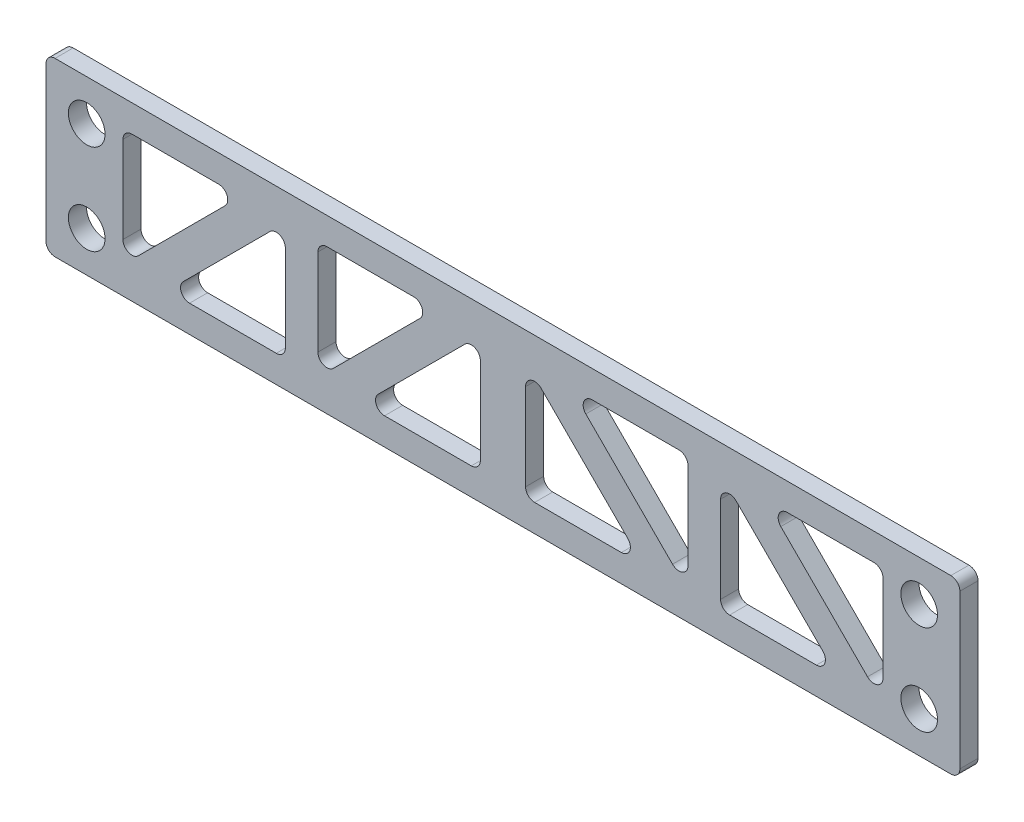
SolidWorks part; units mm, degrees
material "Thornel Mat VMA"
ref_plane "前视基准面" through (0, 0, 0) normal (0, 0, 1) x (1, 0, 0)
ref_plane "上视基准面" through (0, 0, 0) normal (0, 1, 0) x (1, 0, 0)
ref_plane "右视基准面" through (0, 0, 0) normal (1, 0, 0) x (0, 0, -1)
other "Configuration Table"
sketch "草图1" plane through (0, 0, 0) normal (0, 0, 1) x (1, 0, 0)
  line L1 (-46, -5) -> (46, -5) construction
  line L2 (-46, -5) -> (-46, 5) construction
  line L3 (-46, 5) -> (46, 5) construction
  line L4 (46, -5) -> (46, 5) construction
  line L5 (-46, -5) -> (46, 5) construction
  line L6 (-46, 5) -> (46, -5) construction
  line L7 (50.5, -9.5) -> (-50.5, -9.5)
  line L8 (50.5, -9.5) -> (50.5, 9.5)
  line L9 (50.5, 9.5) -> (-50.5, 9.5)
  line L10 (-50.5, -9.5) -> (-50.5, 9.5)
  line L11 (50.5, -9.5) -> (-50.5, 9.5) construction
  line L12 (50.5, 9.5) -> (-50.5, -9.5) construction
  circle A0 centre (-46, 5) radius 2.025
  circle A1 centre (46, 5) radius 2.025
  circle A2 centre (46, -5) radius 2.025
  circle A3 centre (-46, -5) radius 2.025
  point P0 (0, 0)
  point P10 (0, 0)
  dimension "D3" = 4.05
  dimension "D1" = 92
  dimension "D2" = 10
  dimension "D4" = 4.5
  dimension "D5" = 4.5
extrude "凸台-拉伸1" add sketch "草图1" along normal blind 2
sketch "草图2" plane through (0, 0, 2) normal (0, 0, 1) x (1, 0, 0)
  line L0 (-42, 6.5) -> (-42, -6.5)
  line L1 (-42, -6.5) -> (-29, 6.5)
  line L2 (-29, 6.5) -> (-42, 6.5)
  line L3 (-24.0503, 6.5) -> (-37.0503, -6.5)
  line L4 (-37.0503, -6.5) -> (-24.0503, -6.5)
  line L5 (-24.0503, -6.5) -> (-24.0503, 6.5)
  line L6 (-2.5, -6.5) -> (-2.5, 6.5)
  line L7 (50.5, 9.5) -> (-50.5, 9.5) construction
  line L8 (-50.5, -9.5) -> (50.5, -9.5) construction
  line L9 (-42, -6.5) -> (-37.0503, -6.5) construction
  line L10 (-29, 6.5) -> (-24.0503, 6.5) construction
  line L11 (0, 0) -> (50000, 0) construction
  line L12 (-2.5, 6.5) -> (-15.5, -6.5)
  line L13 (-15.5, -6.5) -> (-2.5, -6.5)
  line L14 (-7.4497, 6.5) -> (-20.4497, 6.5)
  line L15 (-20.4497, 6.5) -> (-20.4497, -6.5)
  line L16 (-20.4497, -6.5) -> (-7.4497, 6.5)
  line L41 (0, 0) -> (0, -50000) construction
  line L42 (19.0503, -6.5) -> (19.0503, 6.5) [skipped]
  line L43 (19.0503, 6.5) -> (6.0503, -6.5) [skipped]
  line L44 (14.1005, 6.5) -> (1.1005, 6.5) [skipped]
  line L45 (1.1005, -6.5) -> (14.1005, 6.5) [skipped]
  line L46 (40.6005, -6.5) -> (40.6005, 6.5) [skipped]
  line L47 (40.6005, 6.5) -> (27.6005, -6.5) [skipped]
  line L48 (35.6508, 6.5) -> (22.6508, 6.5) [skipped]
  line L49 (22.6508, 6.5) -> (22.6508, -6.5) [skipped]
  line L50 (22.6508, -6.5) -> (35.6508, 6.5) [skipped]
  line L51 (62.1508, -6.5) -> (62.1508, 6.5) [skipped]
  line L52 (62.1508, 6.5) -> (49.1508, -6.5) [skipped]
  line L53 (57.201, 6.5) -> (44.201, 6.5) [skipped]
  line L54 (44.201, 6.5) -> (44.201, -6.5) [skipped]
  line L55 (44.201, -6.5) -> (57.201, 6.5) [skipped]
  line L56 (83.701, -6.5) -> (83.701, 6.5) [skipped]
  line L57 (83.701, 6.5) -> (70.701, -6.5) [skipped]
  line L58 (78.7513, 6.5) -> (65.7513, 6.5) [skipped]
  line L59 (65.7513, 6.5) -> (65.7513, -6.5) [skipped]
  line L60 (65.7513, -6.5) -> (78.7513, 6.5) [skipped]
  line L61 (6.0503, -6.5) -> (19.0503, -6.5) [skipped]
  line L62 (1.1005, 6.5) -> (1.1005, -6.5) [skipped]
  line L63 (27.6005, -6.5) -> (40.6005, -6.5) [skipped]
  line L64 (49.1508, -6.5) -> (62.1508, -6.5) [skipped]
  line L65 (70.701, -6.5) -> (83.701, -6.5) [skipped]
  line L66 (42, -6.5) -> (29, 6.5)
  line L67 (42, 6.5) -> (42, -6.5)
  line L68 (29, 6.5) -> (42, 6.5)
  line L69 (37.0503, -6.5) -> (24.0503, -6.5)
  line L70 (24.0503, 6.5) -> (37.0503, -6.5)
  line L71 (24.0503, -6.5) -> (24.0503, 6.5)
  line L72 (20.4497, -6.5) -> (7.4497, 6.5)
  line L73 (20.4497, 6.5) -> (20.4497, -6.5)
  line L74 (7.4497, 6.5) -> (20.4497, 6.5)
  line L75 (15.5, -6.5) -> (2.5, -6.5)
  line L76 (2.5, 6.5) -> (15.5, -6.5)
  line L77 (2.5, -6.5) -> (2.5, 6.5)
  circle A0 centre (-46, 5) radius 2.025 construction
  point P15 (-20.1402, 6.5)
  dimension "D1" = 3
  dimension "D2" = 4
  dimension "D4" = 3.5
  dimension "D5" = 2.5
  dimension "D3" = 6
extrude "切除-拉伸1" cut sketch "草图2" against normal blind 2
fillet "圆角1" radius 1 24 edges at (-42, -6.5, 1) (-42, 6.5, 1) (-29, 6.5, 1) (24.0503, -6.5, 1) (24.0503, 6.5, 1) (37.0503, -6.5, 1) (7.4497, 6.5, 1) (20.4497, 6.5, 1) (20.4497, -6.5, 1) (2.5, -6.5, 1) (2.5, 6.5, 1) (15.5, -6.5, 1) (-37.0503, -6.5, 1) (-24.0503, 6.5, 1) (-24.0503, -6.5, 1) (29, 6.5, 1) (42, 6.5, 1) (42, -6.5, 1) (-15.5, -6.5, 1) (-2.5, 6.5, 1) (-7.4497, 6.5, 1) (-20.4497, -6.5, 1) (-20.4497, 6.5, 1) (-2.5, -6.5, 1)
fillet "圆角2" radius 1 4 edges at (50.5, 9.5, 1) (50.5, -9.5, 1) (-50.5, -9.5, 1) (-50.5, 9.5, 1)
